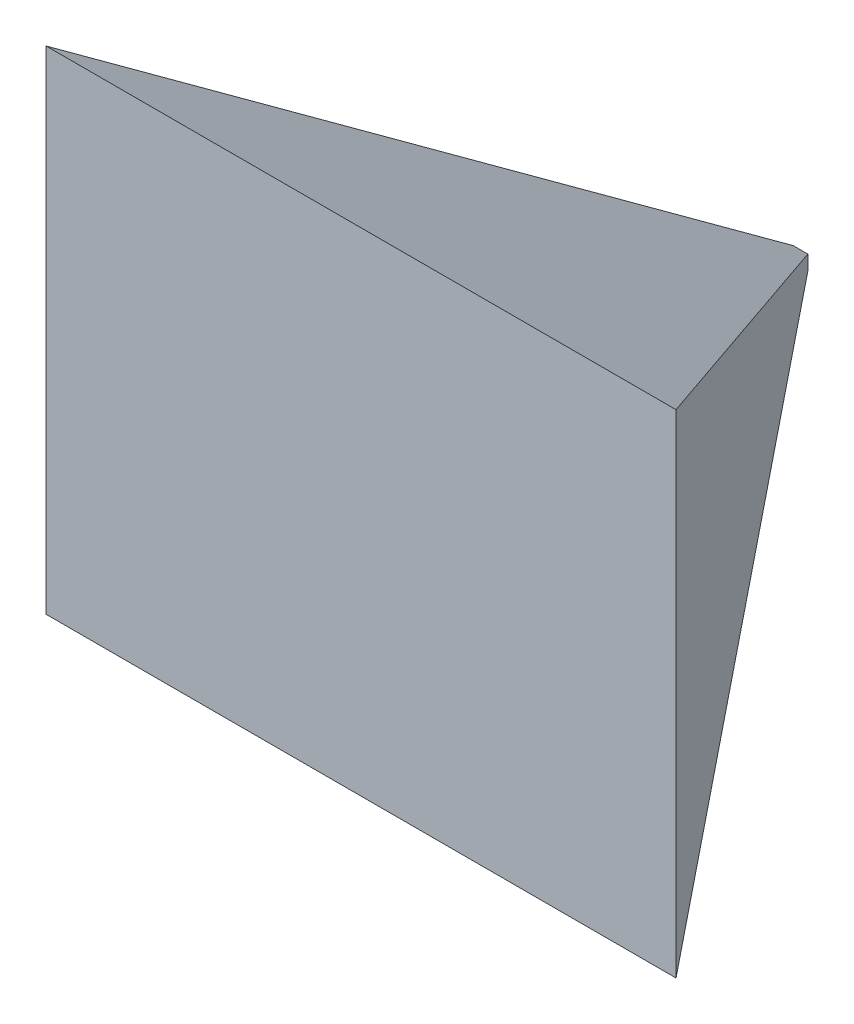
SolidWorks part; units mm, degrees
material "Acrylic (Medium-high impact)"
ref_plane "Front Plane" through (0, 0, 0) normal (0, 0, 1) x (1, 0, 0)
ref_plane "Top Plane" through (0, 0, 0) normal (0, 1, 0) x (1, 0, 0)
ref_plane "Right Plane" through (0, 0, 0) normal (1, 0, 0) x (0, 0, -1)
sketch "Sketch1" plane through (0, 0, 0) normal (0, 0, 1) x (1, 0, 0)
  line L0 (0, -5) -> (0, 5) construction
  line L1 (-5, 5) -> (5, 5)
  line L2 (-5, 5) -> (-5, -5)
  line L3 (-5, -5) -> (5, -5)
  line L4 (5, 5) -> (5, -5)
  line L5 (5, 0) -> (-5, 0) construction
  dimension "D1" = 10
  dimension "D2" = 10
ref_plane "Plane1" through (0, 0, 300) normal (0, 0, 1) x (1, 0, 0)
sketch "Sketch2" plane through (0, 0, 300) normal (0, 0, 1) x (1, 0, 0)
  line L0 (0, -168) -> (0, 0) construction
  line L1 (-215, 168) -> (215, 168)
  line L2 (-215, 168) -> (-215, -168)
  line L3 (-215, -168) -> (215, -168)
  line L4 (215, 168) -> (215, -168)
  line L5 (215, 0) -> (0, 0) construction
  dimension "D1" = 336
  dimension "D2" = 430
loft "Loft1" add profiles "Sketch1", "Sketch2"
